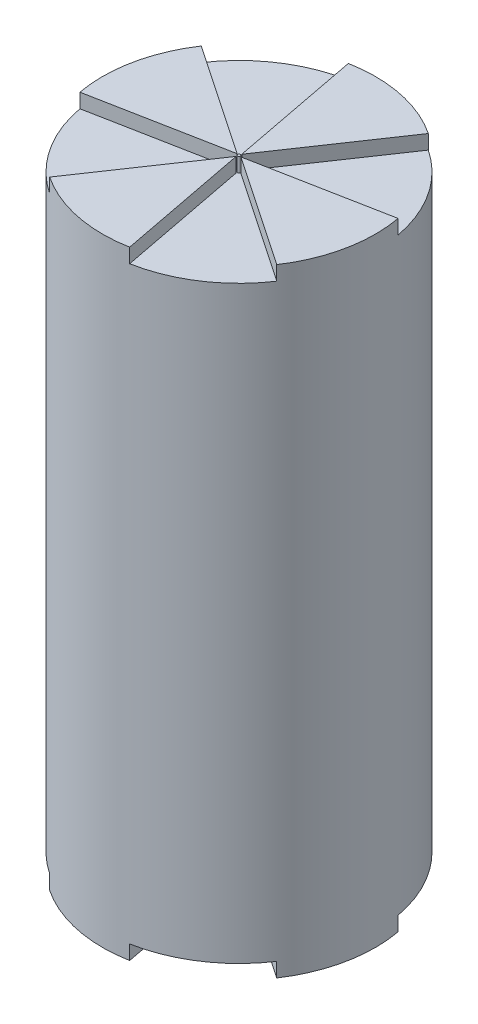
SolidWorks part; units mm, degrees
material "Nylon 101"
ref_plane "Front" through (0, 0, 0) normal (0, 0, 1) x (1, 0, 0)
ref_plane "Top" through (0, 0, 0) normal (0, 1, 0) x (1, 0, 0)
ref_plane "Right" through (0, 0, 0) normal (1, 0, 0) x (0, 0, -1)
sketch "Sketch1" plane through (0, 0, 0) normal (0, 1, 0) x (1, 0, 0)
  circle A0 centre (0, 0) radius 24.13
  dimension "D1" = 48.26
extrude "Boss-Extrude1" add sketch "Sketch1" along normal blind 109.22
sketch "Sketch2" plane through (0, 109.22, 0) normal (0, 1, 0) x (1, 0, 0)
  line L6 (-13.3984, -20.0684) -> (0.0237, -0.2529)
  line L7 (-0.2231, 0.1215) -> (-23.7256, -4.3994)
  arc A6 (-13.3984, -20.0684) -> (-23.7256, -4.3994) centre (0, 0) cw
  arc A7 (0.0237, -0.2529) -> (-0.2231, 0.1215) centre (0, 0) cw
  circle A8 centre (0, 0) radius 24.13 construction
  dimension "D1" = 45
  dimension "D2" = 0.254
extrude "Cut-Extrude7" cut sketch "Sketch2" against normal blind 2.54
pattern_circular "CirPattern2" count 4 over 360 about axis through (0, 0, 0) along (0, 1, 0) of "Cut-Extrude7"
ref_plane "Plane1" through (0, 54.61, 0) normal (0, 1, 0) x (1, 0, 0)
mirror "Mirror1" about plane through (0, 54.61, 0) normal (0, 1, 0) of "CirPattern2", "Cut-Extrude7"
